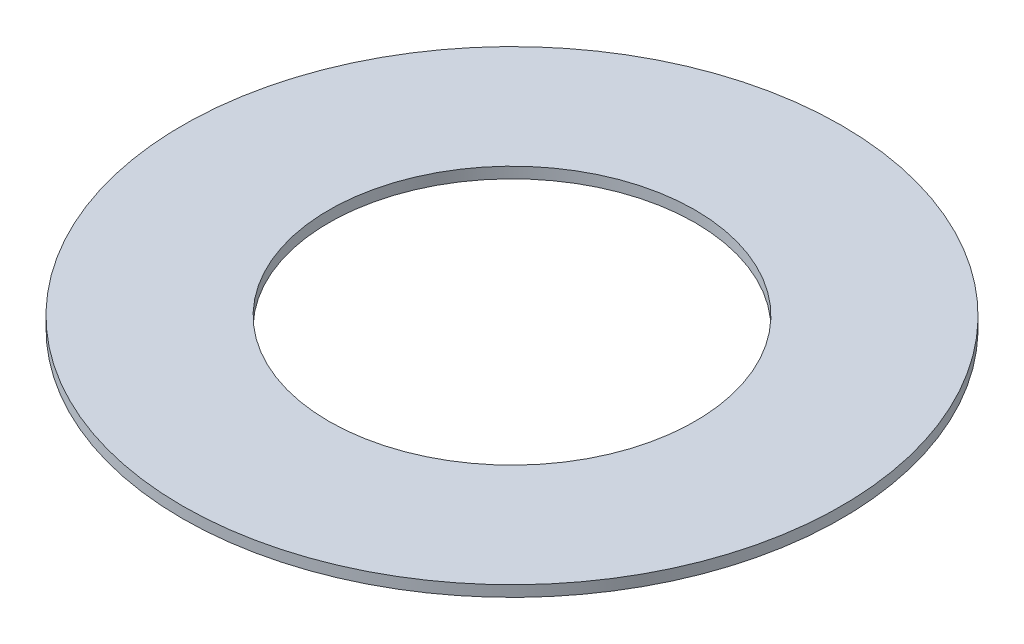
SolidWorks part; units mm, degrees
material "Corrugated Paper"
ref_plane "Front" through (0, 0, 0) normal (0, 0, 1) x (1, 0, 0)
ref_plane "Top" through (0, 0, 0) normal (0, 1, 0) x (1, 0, 0)
ref_plane "Right" through (0, 0, 0) normal (1, 0, 0) x (0, 0, -1)
sketch "Sketch1" plane through (0, 0, 0) normal (0, 1, 0) x (1, 0, 0)
  circle A0 centre (0, 0) radius 9
  circle A1 centre (0, 0) radius 5
  dimension "D1" = 18
  dimension "D2" = 10
extrude "Boss-Extrude1" add sketch "Sketch1" along normal blind 0.3
